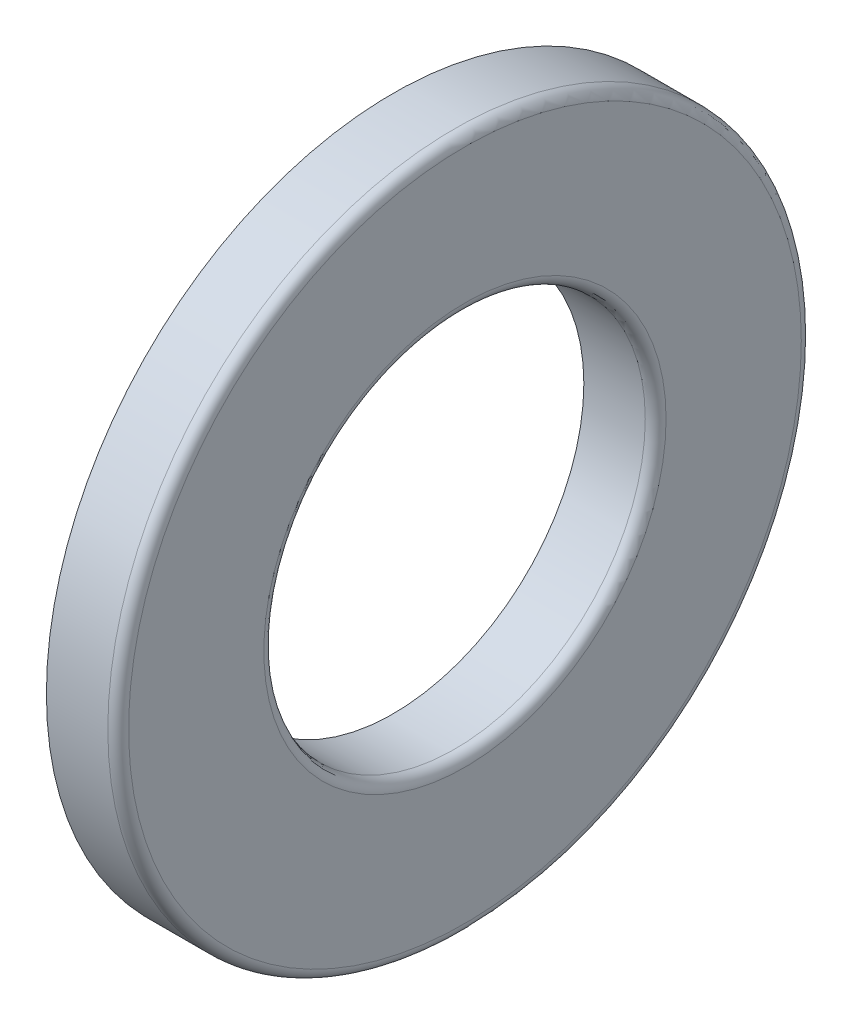
SolidWorks part; units mm, degrees
ref_plane "Alzado" through (0, 0, 0) normal (0, 0, 1) x (1, 0, 0)
ref_plane "Planta" through (0, 0, 0) normal (0, 1, 0) x (1, 0, 0)
ref_plane "Vista lateral" through (0, 0, 0) normal (1, 0, 0) x (0, 0, -1)
ref_plane "Plano1" through (0, 0, 0) normal (0, 0, 1) x (1, 0, 0)
sketch "Croquis1" plane through (0, 0, 0) normal (0, 0, 1) x (1, 0, 0)
  line L0 (9.858, 11) -> (13.4, 11)
  line L1 (14, 11.6) -> (14, 19.4)
  line L2 (13.4, 20) -> (9.858, 20)
  line L3 (9.858, 20) -> (9.858, 17.1427)
  line L4 (9.858, 12.8573) -> (9.858, 11)
  line L5 (13.4, 0) -> (9.858, 0) construction
  arc A0 (13.4, 11) -> (14, 11.6) centre (13.4, 11.6) ccw
  arc A1 (14, 19.4) -> (13.4, 20) centre (13.4, 19.4) ccw
  arc A2 (9.858, 17.1427) -> (9.858, 12.8573) centre (7, 15) cw
revolve "Revolución1" add sketch "Croquis1" angle 360 about L5
